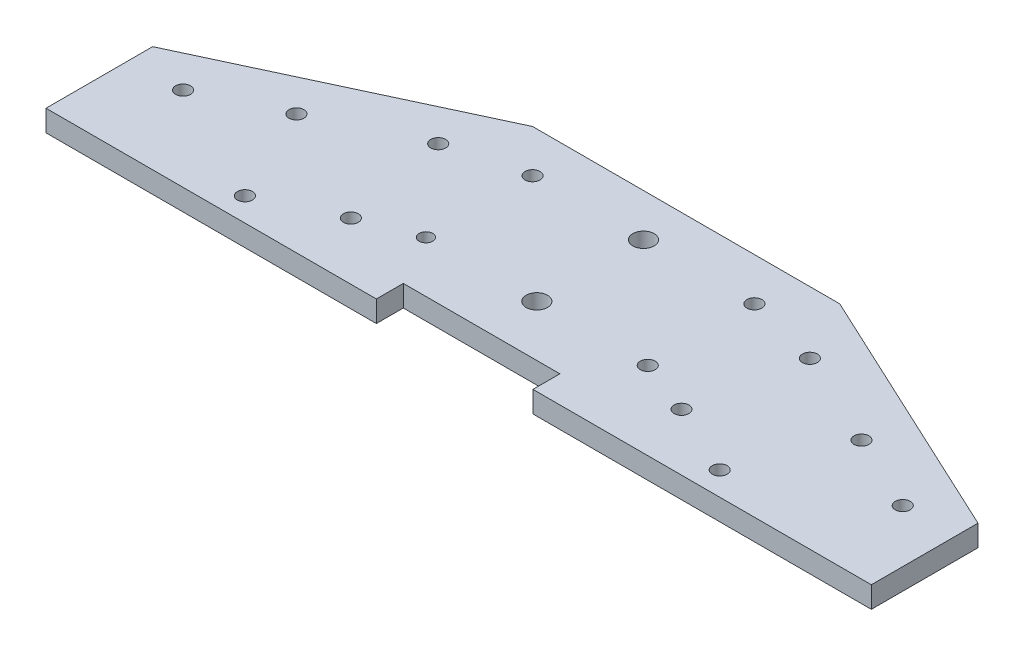
SolidWorks part; units mm, degrees
ref_plane "Alzado" through (0, 0, 0) normal (0, 0, 1) x (1, 0, 0)
ref_plane "Planta" through (0, 0, 0) normal (0, 1, 0) x (1, 0, 0)
ref_plane "Vista lateral" through (0, 0, 0) normal (1, 0, 0) x (0, 0, -1)
sketch "Croquis1" plane through (0, 0, 0) normal (0, 1, 0) x (1, 0, 0)
  line L0 (36, 0) -> (-36, 0)
  line L1 (-36, 0) -> (-96.7226, -28.3154)
  line L2 (36, 0) -> (96.7226, -28.3154)
  line L3 (-96.7226, -28.3154) -> (-96.7226, -53.3154)
  line L4 (-96.7226, -53.3154) -> (96.7226, -53.3154)
  line L5 (96.7226, -53.3154) -> (96.7226, -28.3154)
  point P3 (0, 0)
  dimension "D1" = 72
  dimension "D2" = 155
  dimension "D4" = 155
  dimension "D6" = 25
extrude "Saliente-Extruir1" add sketch "Croquis1" along normal blind 5
sketch "Croquis2" plane through (0, 5, 0) normal (0, 1, 0) x (1, 0, 0)
  circle A0 centre (-84.3397, -33.5749) radius 1.75
  circle A1 centre (-66.2135, -25.1226) radius 1.75
  circle A2 centre (-55.6481, -47.7803) radius 1.75
  circle A3 centre (-38.7013, -39.8779) radius 1.75
  circle A4 centre (-43.5558, -14.5571) radius 1.75
  circle A5 centre (38.8689, -39.956) radius 1.75
  circle A6 centre (55.6481, -47.7803) radius 1.75
  circle A7 centre (84.3397, -33.5749) radius 1.75
  circle A8 centre (66.2135, -25.1226) radius 1.75
  circle A9 centre (43.5558, -14.5571) radius 1.75
  circle A10 centre (0, -10) radius 2.5
  circle A11 centre (0, -35) radius 2.5
  circle A12 centre (26, -10) radius 1.75
  circle A13 centre (26, -35) radius 1.75
  circle A14 centre (-26, -10) radius 1.75
  circle A15 centre (-26, -35) radius 1.5992
extrude "Cortar-Extruir1" cut sketch "Croquis2" against normal up to next
sketch "Croquis3" plane through (0, 5, 0) normal (0, 1, 0) x (1, 0, 0)
  line L0 (-96.7226, -53.3154) -> (96.7226, -53.3154) construction
  line L1 (-19.291, -53.3154) -> (17.409, -53.3154)
  line L2 (-19.291, -53.3154) -> (-19.291, -47)
  line L3 (-19.291, -47) -> (17.409, -47)
  line L4 (17.409, -53.3154) -> (17.409, -47)
extrude "Cortar-Extruir2" cut sketch "Croquis3" against normal blind 10
